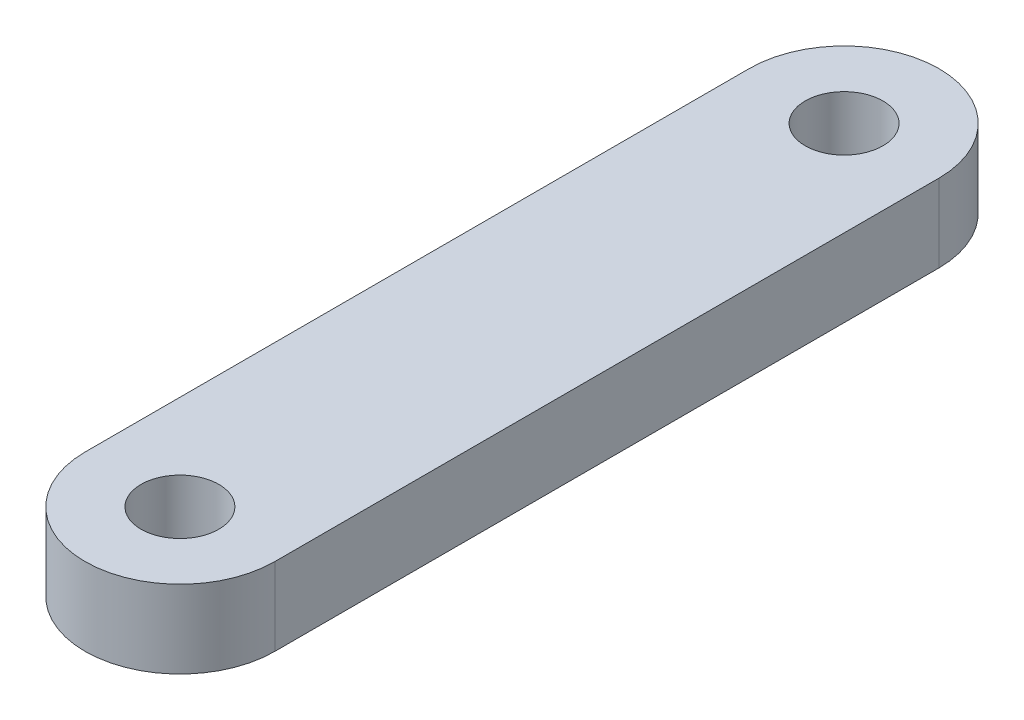
SolidWorks part; units mm, degrees
ref_plane "Front Plane" through (0, 0, 0) normal (0, 0, 1) x (1, 0, 0)
ref_plane "Top Plane" through (0, 0, 0) normal (0, 1, 0) x (1, 0, 0)
ref_plane "Right Plane" through (0, 0, 0) normal (1, 0, 0) x (0, 0, -1)
sketch "Sketch1" plane through (0, 0, 0) normal (0, 1, 0) x (1, 0, 0)
  line L0 (0, 0) -> (0, 35.56) construction
  line L1 (-5.08, 0) -> (-5.08, 35.56)
  line L2 (5.08, 0) -> (5.08, 35.56)
  arc A0 (-5.08, 0) -> (5.08, 0) centre (0, 0) ccw
  arc A1 (5.08, 35.56) -> (-5.08, 35.56) centre (0, 35.56) ccw
  circle A2 centre (0, 35.56) radius 2.0828
  circle A3 centre (0, 0) radius 2.0828
  point P3 (0, 17.78)
  dimension "D1" = 4.1656
  dimension "D2" = 4.1656
  dimension "D3" = 10.16
  dimension "D4" = 35.56
extrude "Boss-Extrude1" add sketch "Sketch1" along normal blind 4.1656
